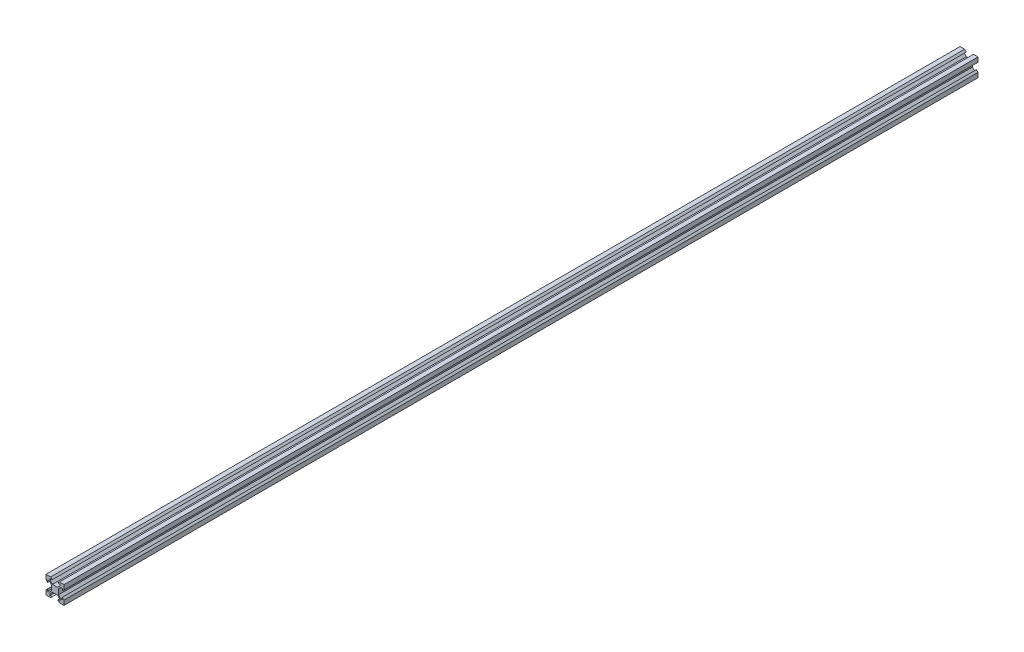
SolidWorks part; units mm, degrees
ref_plane "Front Plane" through (0, 0, 0) normal (0, 0, 1) x (1, 0, 0)
ref_plane "Top Plane" through (0, 0, 0) normal (0, 1, 0) x (1, 0, 0)
ref_plane "Right Plane" through (0, 0, 0) normal (1, 0, 0) x (0, 0, -1)
sketch "Sketch1" plane through (0, 0, 0) normal (0, 0, 1) x (1, 0, 0)
  line L1 (0, 0) -> (20, 0)
  line L2 (0, 0) -> (0, 20)
  line L3 (0, 20) -> (20, 20)
  line L4 (20, 0) -> (20, 20)
  line L5 (0, 0) -> (20, 20) construction
  line L6 (0, 20) -> (20, 0) construction
  point P4 (10, 10)
  dimension "D1" = 20
  dimension "D2" = 20
extrude "Boss-Extrude1" add sketch "Sketch1" along normal blind 1014.98
sketch "Sketch2" plane through (0, 0, 1014.98) normal (0, 0, 1) x (1, 0, 0)
  line L4 (0, 0) -> (20, 20) construction
  line L5 (4.5, 18.18) -> (6.94, 18.18)
  line L6 (4.5, 16.4758) -> (4.5, 18.18)
  line L15 (7.1658, 13.81) -> (4.5, 16.4758)
  line L17 (12.8342, 13.81) -> (7.1658, 13.81)
  line L27 (15.5, 16.4758) -> (12.8342, 13.81)
  line L29 (15.5, 18.18) -> (15.5, 16.4758)
  line L31 (13.06, 18.18) -> (15.5, 18.18)
  line L33 (14.88, 20) -> (5.12, 20)
  line L35 (6.94, 18.18) -> (5.12, 20)
  line L54 (14.88, 20) -> (13.06, 18.18)
  line L56 (14.88, 0) -> (13.06, 1.82)
  line L57 (6.94, 1.82) -> (5.12, 0)
  line L58 (14.88, 0) -> (5.12, 0)
  line L68 (13.06, 1.82) -> (15.5, 1.82)
  line L71 (15.5, 1.82) -> (15.5, 3.5242)
  line L81 (15.5, 3.5242) -> (12.8342, 6.19)
  line L82 (12.8342, 6.19) -> (7.1658, 6.19)
  line L83 (7.1658, 6.19) -> (4.5, 3.5242)
  line L84 (4.5, 3.5242) -> (4.5, 1.82)
  line L85 (4.5, 1.82) -> (6.94, 1.82)
  line L136 (20, 0) -> (10, 0) construction
  line L137 (0, 0) -> (20, 0) construction
  line L186 (1.82, 4.5) -> (1.82, 6.94)
  line L187 (3.5242, 4.5) -> (1.82, 4.5)
  line L188 (6.19, 7.1658) -> (3.5242, 4.5)
  line L189 (6.19, 12.8342) -> (6.19, 7.1658)
  line L190 (3.5242, 15.5) -> (6.19, 12.8342)
  line L191 (1.82, 15.5) -> (3.5242, 15.5)
  line L192 (1.82, 13.06) -> (1.82, 15.5)
  line L193 (0, 14.88) -> (0, 5.12)
  line L194 (1.82, 6.94) -> (0, 5.12)
  line L195 (0, 14.88) -> (1.82, 13.06)
  line L203 (20, 14.88) -> (18.18, 13.06)
  line L205 (18.18, 6.94) -> (20, 5.12)
  line L206 (20, 14.88) -> (20, 5.12)
  line L207 (18.18, 13.06) -> (18.18, 15.5)
  line L208 (18.18, 15.5) -> (16.4758, 15.5)
  line L209 (16.4758, 15.5) -> (13.81, 12.8342)
  line L210 (13.81, 12.8342) -> (13.81, 7.1658)
  line L211 (13.81, 7.1658) -> (16.4758, 4.5)
  line L212 (16.4758, 4.5) -> (18.18, 4.5)
  line L213 (18.18, 4.5) -> (18.18, 6.94)
extrude "Cut-Extrude1" cut sketch "Sketch2" against normal through all
